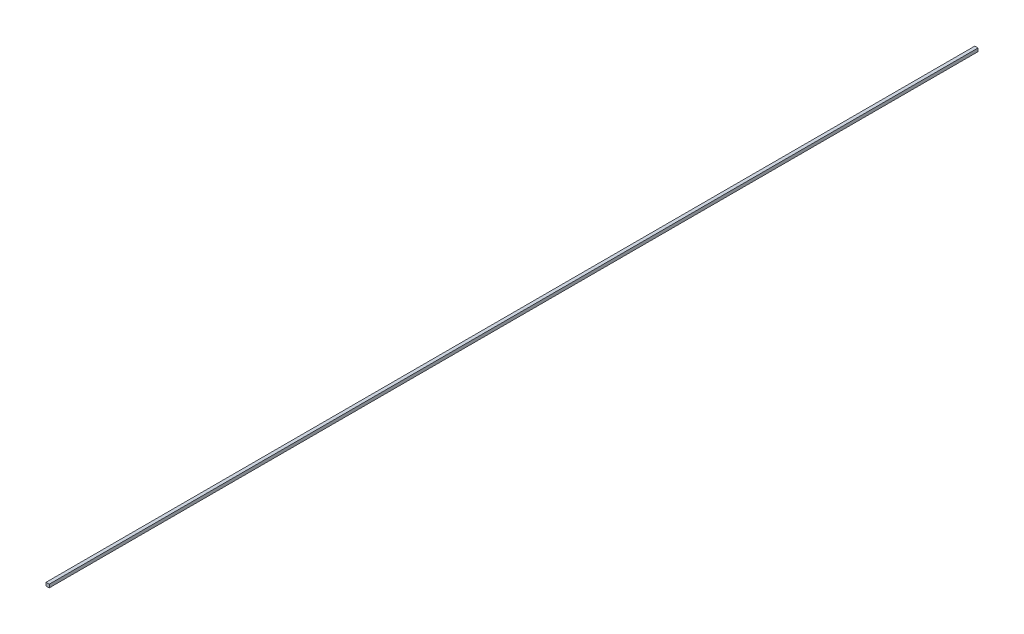
SolidWorks part; units mm, degrees
ref_plane "Plano frontal" through (0, 0, 0) normal (0, 0, 1) x (1, 0, 0)
ref_plane "Plano superior" through (0, 0, 0) normal (0, 1, 0) x (1, 0, 0)
ref_plane "Plano direito" through (0, 0, 0) normal (1, 0, 0) x (0, 0, -1)
sketch "Esboço1" plane through (0, 0, 0) normal (0, 0, 1) x (1, 0, 0)
  line L2 (-0.175, 0.175) -> (0.175, 0.175)
  line L3 (-0.175, 0.175) -> (-0.175, -0.175)
  line L4 (-0.175, -0.175) -> (0.175, -0.175)
  line L5 (0.175, 0.175) -> (0.175, -0.175)
  line L6 (-0.175, 0.175) -> (0.175, -0.175) construction
  line L7 (-0.175, -0.175) -> (0.175, 0.175) construction
  point P0 (0, 0)
  dimension "D1" = 0.35
extrude "Ressalto-extrusão1" add sketch "Esboço1" along normal blind 100
